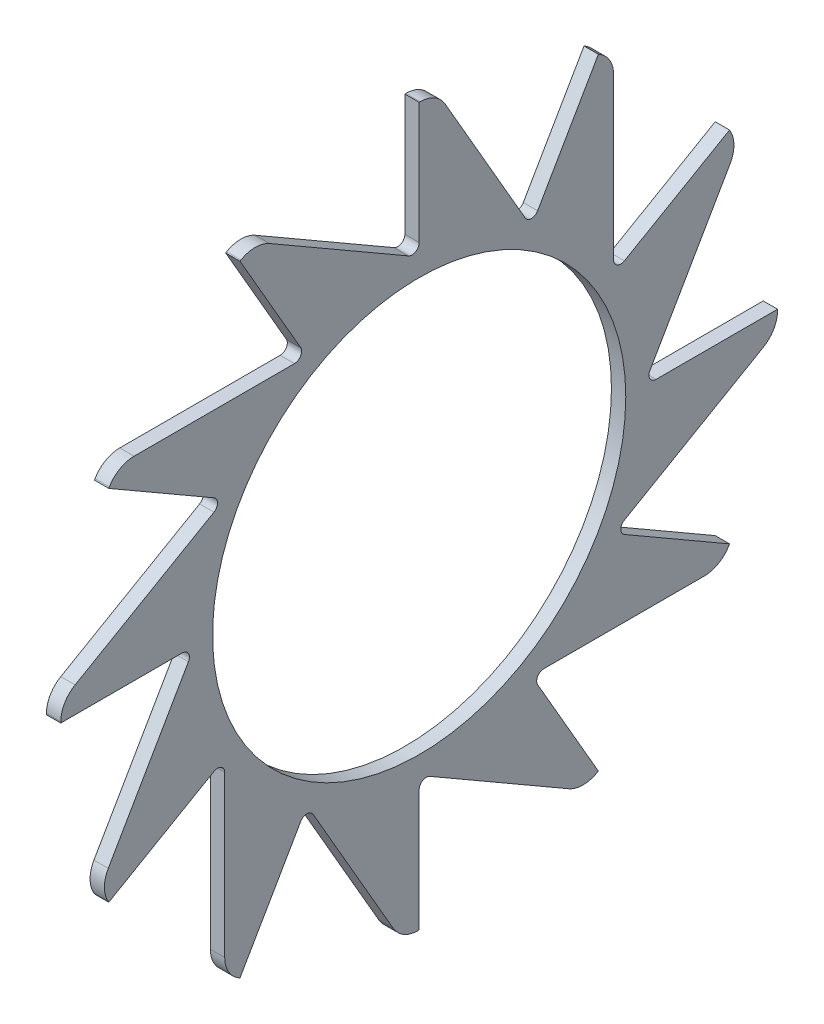
SolidWorks part; units mm, degrees
material "Acier S235"
ref_plane "Plan de face" through (0, 0, 0) normal (0, 0, 1) x (1, 0, 0)
ref_plane "Plan de dessus" through (0, 0, 0) normal (0, 1, 0) x (1, 0, 0)
ref_plane "Plan de droite" through (0, 0, 0) normal (1, 0, 0) x (0, 0, -1)
sketch "Esquisse10" plane through (0, 0, 0) normal (1, 0, 0) x (0, 0, -1)
  circle A0 centre (0, 0) radius 57.65
  circle A2 centre (0, 0) radius 100
  dimension "D1" = 115.3
  dimension "D2" = 200
extrude "Boss.-Extru.1" add sketch "Esquisse10" against normal mid plane 4 separate body
sketch "Esquisse11" plane through (0, 0, 0) normal (1, 0, 0) x (0, 0, -1)
  line L0 (-45.6191, 88.9882) -> (0, 62.65)
  line L1 (0, 62.65) -> (0, 100)
  circle A1 centre (0, 0) radius 100
  circle A3 centre (0, 0) radius 100 construction
  circle A4 centre (0, 0) radius 57.65 construction
  dimension "D1" = 5
  dimension "D2" = 60
extrude "Enlèv. mat.-Extru.3" cut sketch "Esquisse11" against normal through all both and the other way through all
fillet "Congé3" radius 8 1 edges at (0, 88.9882, 45.6191)
fillet "Congé4" radius 2 1 edges at (0, 62.65, 0)
pattern_circular "Répétition circulaire4" count 12 over 360 about axis through (0, 0, 0) along (1, 0, 0) of "Congé3", "Enlèv. mat.-Extru.3", "Congé4"
sheet metal parameters "Tôlerie30" thickness 4 parameters "D1"=1
flat pattern "Etat déplié42"
sketch "Lignes de pliage2" plane through (0, 0, 0) normal (0, 1, 0) x (1, 0, 0)
sketch3d "Cube de visualisation2" [suppressed]
  line L0 (-71.5741, -121.9719, 0) -> (121.9719, -71.574, 0) construction
  line L1 (-121.1588, 68.4512, 0) -> (72.3872, 118.8491, 0) construction
  line L2 (-71.5741, -121.9719, 0) -> (-121.1588, 68.4512, 0) construction
  line L3 (121.9719, -71.574, 0) -> (72.3872, 118.8491, 0) construction
sheet metal parameters "Tôlerie44" thickness 4 parameters "D1"=1
flat pattern "Etat déplié42"
sketch "Lignes de pliage2" plane through (0, 0, 0) normal (0, 1, 0) x (1, 0, 0)
sketch3d "Cube de visualisation2" [suppressed]
  line L0 (99.8748, 100.1249, 0) -> (100.1248, -99.8749, 0) construction
  line L1 (-100.1249, 99.8749, 0) -> (-99.8749, -100.1249, 0) construction
  line L2 (99.8748, 100.1249, 0) -> (-100.1249, 99.8749, 0) construction
  line L3 (100.1248, -99.8749, 0) -> (-99.8749, -100.1249, 0) construction
